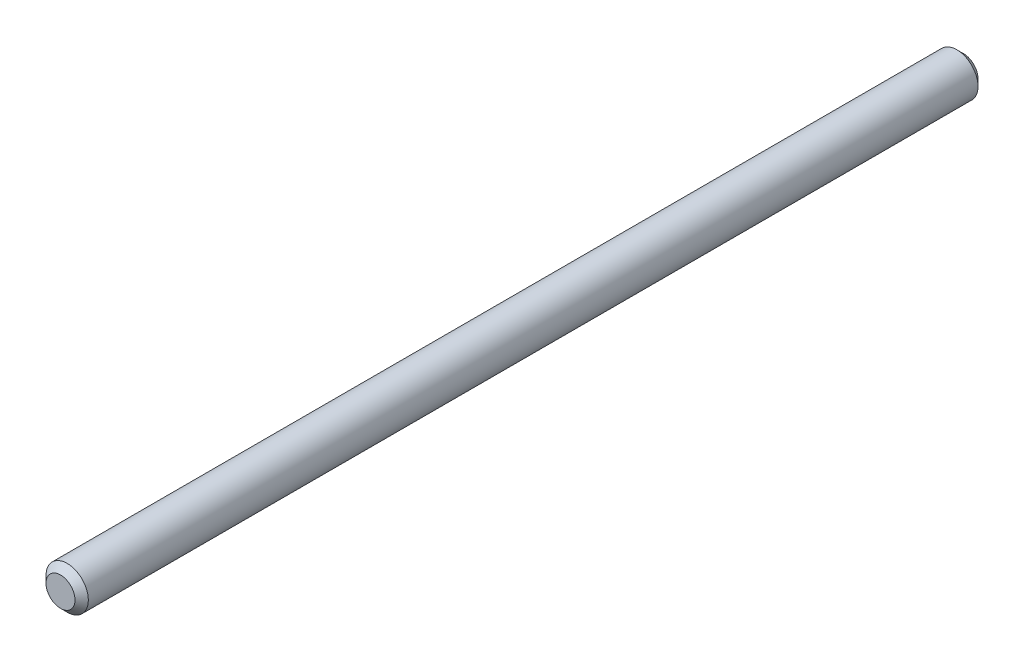
SolidWorks part; units mm, degrees
material "AISI 1020"
ref_plane "Front Plane" through (0, 0, 0) normal (0, 0, 1) x (1, 0, 0)
ref_plane "Top Plane" through (0, 0, 0) normal (0, 1, 0) x (1, 0, 0)
ref_plane "Right Plane" through (0, 0, 0) normal (1, 0, 0) x (0, 0, -1)
sketch "Sketch1" plane through (0, 0, 0) normal (0, 0, 1) x (1, 0, 0)
  circle A0 centre (0, 0) radius 3.175
  dimension "D1" = 6.35
extrude "Boss-Extrude1" add sketch "Sketch1" against normal blind 135.47
cosmetic thread "Cosmetic Thread1"
chamfer "Chamfer1" distance 1 angle 45 2 edges at (3.175, 0, -135.47) (3.175, 0, 0)
